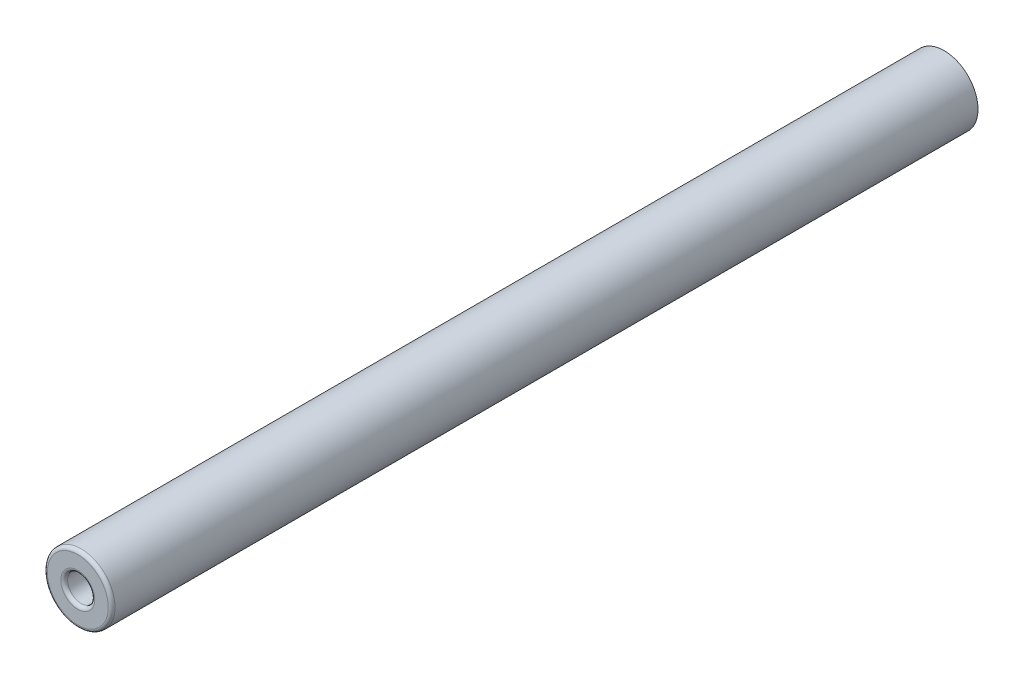
SolidWorks part; units mm, degrees
material "Acero aleado"
ref_plane "Plane1" through (0, 0, 0) normal (0, 0, 1) x (1, 0, 0)
ref_plane "Plane2" through (0, 0, 0) normal (0, 1, 0) x (1, 0, 0)
ref_plane "Plane3" through (0, 0, 0) normal (1, 0, 0) x (0, 0, -1)
sketch "Sketch1" plane through (0, 0, 0) normal (0, 0, 1) x (1, 0, 0)
  circle A0 centre (0, 0) radius 2.5
  dimension "D1" = 5
extrude "Extrude1" add sketch "Sketch1" along normal blind 64
sketch "Sketch2" plane through (0, 0, 64) normal (0, 0, 1) x (1, 0, 0)
  circle A0 centre (0, 0) radius 1
  dimension "D1" = 2
extrude "ICE1" cut sketch "Sketch2" against normal blind 10
fillet "Fillet1" radius 0.25 2 edges at (2.5, 0, 64) (1, 0, 64)
